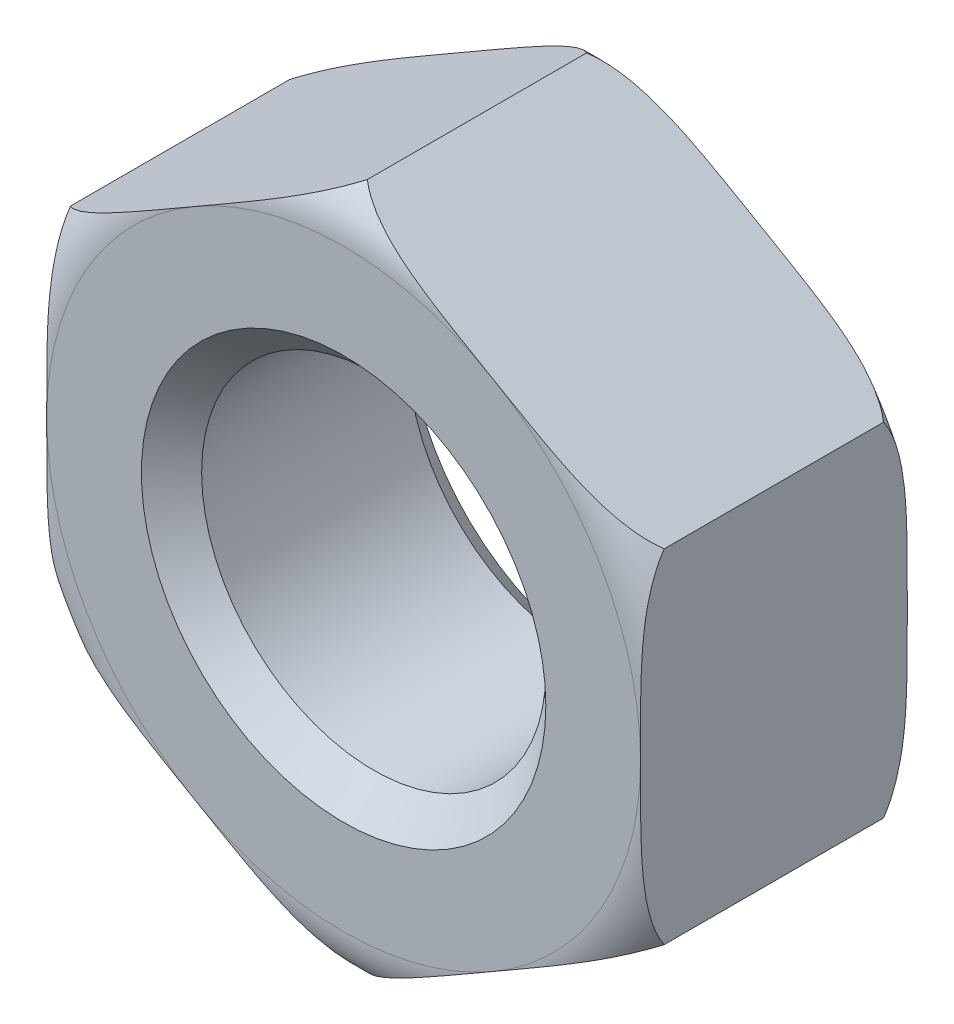
SolidWorks part; units mm, degrees
ref_plane "Front Plane" through (0, 0, 0) normal (0, 0, 1) x (1, 0, 0)
ref_plane "Top Plane" through (0, 0, 0) normal (0, 1, 0) x (1, 0, 0)
ref_plane "Right Plane" through (0, 0, 0) normal (1, 0, 0) x (0, 0, -1)
sketch "Sketch1" plane through (0, 0, 0) normal (0, 0, 1) x (1, 0, 0)
  line L1 (3.45, 1.9919) -> (0, 3.9837)
  line L2 (0, 3.9837) -> (-3.45, 1.9919)
  line L3 (-3.45, 1.9919) -> (-3.45, -1.9919)
  line L4 (-3.45, -1.9919) -> (0, -3.9837)
  line L5 (0, -3.9837) -> (3.45, -1.9919)
  line L6 (3.45, -1.9919) -> (3.45, 1.9919)
  circle A0 centre (0, 0) radius 3.45 construction
  circle A1 centre (0, 0) radius 2
  dimension "D1" = 4
  dimension "D2" = 6.9
extrude "Boss-Extrude1" add sketch "Sketch1" along normal blind 3.1
chamfer "Chamfer1" distance 0.35 angle 45 2 edges at (2, 0, 0) (2, 0, 3.1)
sketch "Sketch2" plane through (0, 0, 0) normal (0, 1, 0) x (1, 0, 0)
  line L0 (0, 0) -> (-3.45, 0) construction
  line L1 (-3.45, -3.1) -> (-3.45, 0) construction
  line L2 (0, -1.55) -> (-3.45, -1.55) construction
  line L3 (0, -3.1) -> (0, 0) construction
  line L4 (0, -1.55) -> (0, 1.437) construction
  line L5 (-4, -0.3) -> (-4.5008, -0.3)
  line L6 (-4.5008, -0.3) -> (-4.5008, 0.3612)
  line L7 (-4.5008, 0.3612) -> (-3.45, 0.3612)
  line L8 (-3.45, 0.3612) -> (-3.45, 0)
  line L9 (-3.45, -3.4612) -> (-3.45, -3.1)
  line L10 (-4.5008, -3.4612) -> (-3.45, -3.4612)
  line L11 (-4.5008, -2.8) -> (-4.5008, -3.4612)
  line L12 (-4, -2.8) -> (-4.5008, -2.8)
  arc A0 (-4, -0.3) -> (-3.45, 0) centre (-3.45, -0.6542) cw
  arc A1 (-4, -2.8) -> (-3.45, -3.1) centre (-3.45, -2.4458) ccw
  dimension "D1" = 0.3
  dimension "D2" = 4
revolve "Cut-Revolve1" cut sketch "Sketch2" angle 360 about L4
